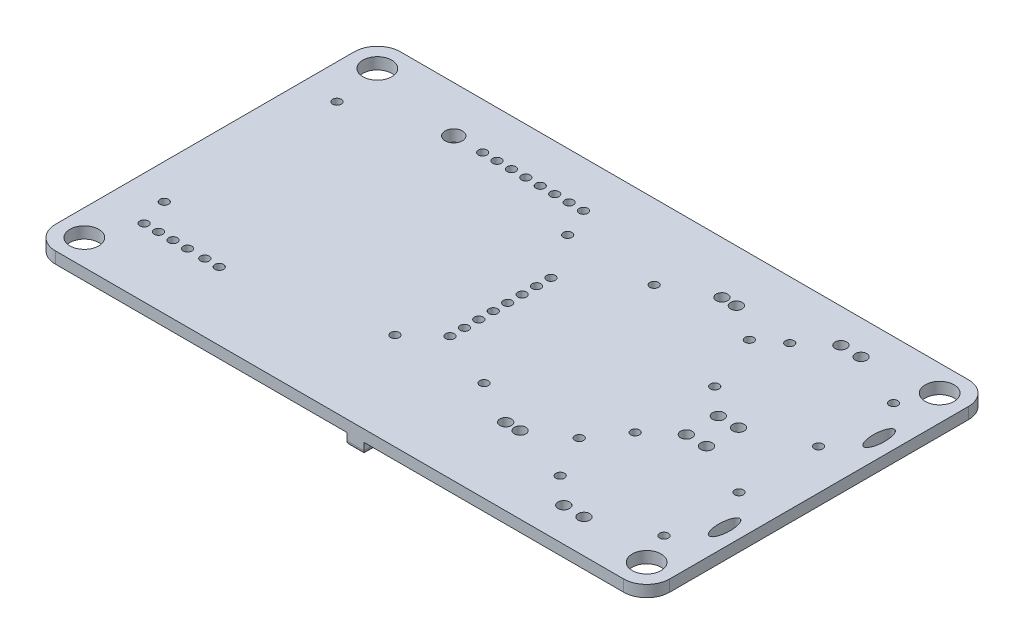
SolidWorks part; units mm, degrees
ref_plane "Front Plane" through (0, 0, 0) normal (0, 0, 1) x (1, 0, 0)
ref_plane "Top Plane" through (0, 0, 0) normal (0, 1, 0) x (1, 0, 0)
ref_plane "Right Plane" through (0, 0, 0) normal (1, 0, 0) x (0, 0, -1)
sketch "Sketch1" plane through (0, 0, 0) normal (0, 1, 0) x (1, 0, 0)
  line L1 (0, 0) -> (213, 0)
  line L2 (0, 0) -> (0, 119.6)
  line L3 (0, 119.6) -> (213, 119.6)
  line L4 (213, 0) -> (213, 119.6)
  circle A0 centre (12, 93.6) radius 1.5
  circle A1 centre (12.1136, 33.6001) radius 1.5
  circle A2 centre (92, 93.6) radius 1.5
  circle A3 centre (92.1136, 33.6001) radius 1.5
  circle A4 centre (87.5, 103.6) radius 1.5
  circle A12 centre (102, 77.8) radius 1.5
  circle A14 centre (82.5, 103.6) radius 1.5
  circle A15 centre (77.5, 103.6) radius 1.5
  circle A16 centre (72.5, 103.6) radius 1.5
  circle A17 centre (67.5, 103.6) radius 1.5
  circle A18 centre (62.5, 103.6) radius 1.5
  circle A19 centre (57.5, 103.6) radius 1.5
  circle A20 centre (52.5, 103.6) radius 1.5
  circle A21 centre (102, 72.8) radius 1.5
  circle A22 centre (102, 67.8) radius 1.5
  circle A23 centre (102, 62.8) radius 1.5
  circle A24 centre (102, 57.8) radius 1.5
  circle A25 centre (102, 52.8) radius 1.5
  circle A26 centre (102, 47.8) radius 1.5
  circle A27 centre (102, 42.8) radius 1.5
  circle A28 centre (122, 93.6) radius 1.5
  circle A29 centre (155, 93.6) radius 1.5
  circle A32 centre (122, 34.6) radius 1.5
  circle A33 centre (155, 34.6) radius 1.5
  circle A38 centre (15.1136, 23.6001) radius 1.5
  circle A39 centre (20.1378, 23.6001) radius 1.5
  circle A40 centre (25.1621, 23.6001) radius 1.5
  circle A41 centre (30.1863, 23.6001) radius 1.5
  circle A42 centre (36.1863, 23.6001) radius 1.5
  circle A43 centre (41.1863, 23.6001) radius 1.5
  circle A44 centre (137.5, 101.6) radius 2
  circle A45 centre (142.5, 101.6) radius 2
  circle A46 centre (137.5, 26.6) radius 2
  circle A47 centre (142.5, 26.6) radius 2
  circle A64 centre (9, 110.6) radius 5
  circle A65 centre (9, 9) radius 5
  circle A66 centre (204, 110.6) radius 5
  circle A67 centre (204, 9) radius 5
  dimension "D1" = 12
  dimension "D5" = 80
  dimension "D7" = 60
  dimension "D12" = 8
  dimension "D13" = 15.8
  dimension "D15" = 33
  dimension "D16" = 59
  dimension "D17" = 33
  dimension "D23" = 3
  dimension "D26" = 6
  dimension "D30" = 8
  dimension "D31" = 5
  dimension "D72" = 9
  dimension "D76" = 9
  dimension "D64" = 30
  dimension "D19" = 195
  dimension "D2" = 26
  dimension "D4" = 60
  dimension "D8" = 80
  dimension "D9" = 10
  dimension "D10" = 4.5
  dimension "D11" = 8
  dimension "D14" = 10
  dimension "D18" = 59
  dimension "D20" = 9
  dimension "D24" = 10
  dimension "D28" = 15.5
  dimension "D29" = 5
  dimension "D32" = 15.5
  dimension "D33" = 8
  dimension "D56" = 9
  dimension "D61" = 0
  dimension "D65" = 9
  dimension "D66" = 101.6
  dimension "D67" = 0
  dimension "D68" = 0
  dimension "D69" = 0
  dimension "D70" = 0
  dimension "D73" = 9
  dimension "D75" = 9
  dimension "D77" = 9
  dimension "D25" = 4
  dimension "D27" = 2
extrude "Boss-Extrude1" add sketch "Sketch1" along normal blind 4 contours L1 L4 L3 L2
sketch "Sketch5" plane through (0, 4, 0) normal (0, 1, 0) x (1, 0, 0)
  line L0 (213, 119.6) -> (0, 119.6) construction
  line L1 (0, 0) -> (213, 0) construction
  circle A0 centre (199.0044, 99.6) radius 1.5
  circle A1 centre (199.0069, 73.6) radius 1.5
  circle A2 centre (163.0045, 99.5966) radius 1.5
  circle A3 centre (163.0069, 73.5966) radius 1.5
  circle A4 centre (172.5, 107.8462) radius 2
  circle A5 centre (179.5, 107.8462) radius 2
  circle A6 centre (172.5069, 65.3466) radius 2
  circle A7 centre (179.5069, 65.3466) radius 2
  circle A8 centre (199.0113, 46) radius 1.5
  circle A9 centre (199.0138, 20) radius 1.5
  circle A10 centre (163.0113, 45.9966) radius 1.5
  circle A11 centre (163.0138, 19.9966) radius 1.5
  circle A12 centre (172.5069, 54.2462) radius 2
  circle A13 centre (179.5069, 54.2462) radius 2
  circle A14 centre (172.5138, 11.7466) radius 2
  circle A15 centre (179.5138, 11.7466) radius 2
  circle A16 centre (142.5, 101.6) radius 2 construction
  ellipse E0 centre (207.0045, 86.5966) end of major axis (207.0045, 81.2932) minor radius 2
  ellipse E1 centre (207.0113, 32.9966) end of major axis (207.0113, 27.6932) minor radius 2
  point P24 (225.3334, 59.6134)
  dimension "D11" = 8.2496
  dimension "D12" = 8.2496
  dimension "D13" = 8.25
  dimension "D14" = 8.25
  dimension "D15" = 8
  dimension "D16" = 7.9976
  dimension "D35" = 0
  dimension "D36" = 20
  dimension "D37" = 20
  dimension "D38" = 30
  dimension "D1" = 44.4072
  dimension "D2" = 44.4072
  dimension "D3" = 26
  dimension "D4" = 26
  dimension "D5" = 36
  dimension "D6" = 36
  dimension "D7" = 9.5
  dimension "D8" = 9.4955
  dimension "D9" = 7
  dimension "D10" = 7
  dimension "D17" = 13.0034
  dimension "D18" = 44.4072
  dimension "D19" = 44.4072
  dimension "D20" = 26
  dimension "D21" = 26
  dimension "D22" = 36
  dimension "D23" = 36
  dimension "D24" = 9.5
  dimension "D25" = 9.4955
  dimension "D26" = 7
  dimension "D27" = 7
  dimension "D28" = 8.2496
  dimension "D29" = 8.2496
  dimension "D30" = 8.25
  dimension "D31" = 8.25
  dimension "D32" = 8
  dimension "D33" = 7.9976
  dimension "D34" = 13.0034
extrude "Cut-Extrude1" cut sketch "Sketch5" against normal blind 4
sketch "Sketch6" plane through (0, 4, 0) normal (0, 1, 0) x (1, 0, 0)
  circle A0 centre (42.5, 103.6) radius 3
  circle A1 centre (52.5, 103.6) radius 1.5 construction
  point P6 (46.5056, 103.0385)
  dimension "D1" = 0
  dimension "D2" = 10
extrude "Cut-Extrude2" cut sketch "Sketch6" against normal blind 4
sketch "Sketch7" plane through (0, 0, 0) normal (0, -1, 0) x (1, 0, 0)
  line L1 (0, 0) -> (213, 0) construction
  line L2 (109, 0) -> (115, 0)
  line L3 (109, 0) -> (109, -119.6)
  line L4 (109, -119.6) -> (115, -119.6)
  line L5 (115, 0) -> (115, -119.6)
  line L6 (213, -119.6) -> (0, -119.6) construction
  line L7 (0, -119.6) -> (0, 0) construction
  line L8 (109, -86.6) -> (0, -86.6)
  line L9 (109, -86.6) -> (109, -83.0772)
  line L10 (109, -83.0772) -> (0, -83.0772)
  line L11 (0, -86.6) -> (0, -83.0772)
  line L13 (115, -83.0772) -> (197.9577, -83.0772)
  line L14 (115, -83.0772) -> (115, -86.6)
  line L15 (115, -86.6) -> (197.9577, -86.6)
  line L16 (197.9577, -83.0772) -> (197.9577, -86.6)
  circle A0 centre (122, -34.6) radius 1.5 construction
  circle A1 centre (102, -42.8) radius 1.5 construction
  circle A2 centre (12, -93.6) radius 1.5 construction
  dimension "D2" = 7
  dimension "D3" = 7
  dimension "D1" = 7
extrude "Boss-Extrude2" add sketch "Sketch7" along normal blind 4 contours L11 L8 L3 L10 | L5 L2 L3 L4 | L16 L13 L5 L15
fillet "Fillet7" radius 1.5 12 edges at (0, -4, -84.8386) (54.5, -4, -86.6) (115, -4, -103.1) (197.9577, -4, -84.8386) (156.4788, -4, -83.0772) (115, -4, -41.5386) (112, -4, 0) (109, -4, -103.1) (112, -4, -119.6) (156.4788, -4, -86.6) (109, -4, -41.5386) (54.5, -4, -83.0772)
fillet "Fillet8" radius 8 1 edges at (0, 2, -119.6)
fillet "Fillet9" radius 8 1 edges at (213, 2, -119.6)
fillet "Fillet10" radius 8 1 edges at (213, 2, 0)
fillet "Fillet11" radius 8 1 edges at (0, 2, 0)
